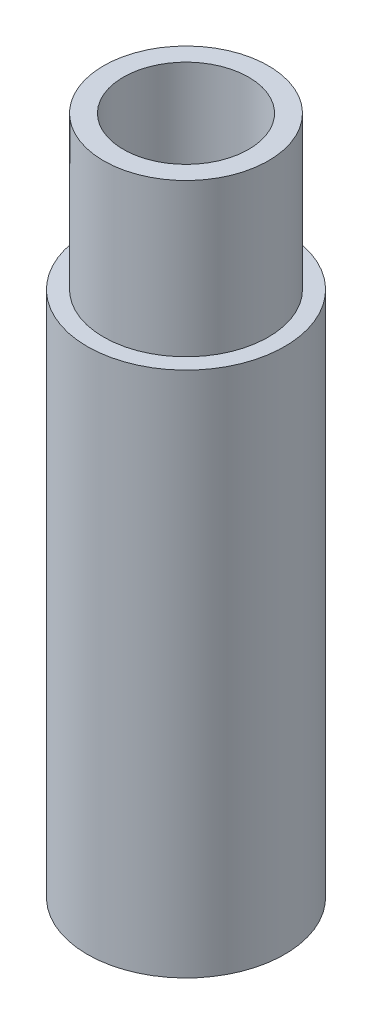
SolidWorks part; units mm, degrees
material "AISI 304"
ref_plane "Front Plane" through (0, 0, 0) normal (0, 0, 1) x (1, 0, 0)
ref_plane "Top Plane" through (0, 0, 0) normal (0, 1, 0) x (1, 0, 0)
ref_plane "Right Plane" through (0, 0, 0) normal (1, 0, 0) x (0, 0, -1)
sketch "Sketch1" plane through (0, 0, 0) normal (0, 1, 0) x (1, 0, 0)
  circle A0 centre (0, 0) radius 4.7625
  dimension "D1" = 9.525
extrude "Boss-Extrude1" add sketch "Sketch1" along normal blind 25.4
sketch "Sketch2" plane through (0, 25.4, 0) normal (0, 1, 0) x (1, 0, 0)
  circle A0 centre (0, 0) radius 3.9751
  dimension "D1" = 7.9502
extrude "Boss-Extrude2" add sketch "Sketch2" along normal blind 7.366
sketch "Sketch3" plane through (0, 0, 0) normal (0, -1, 0) x (1, 0, 0)
  circle A0 centre (0, 0) radius 3.0226
  dimension "D1" = 6.0452
extrude "Cut-Extrude1" cut sketch "Sketch3" against normal through all
sketch "Sketch4" plane through (0, 0, 0) normal (0, -1, 0) x (1, 0, 0)
  circle A0 centre (0, 0) radius 3.4544
  dimension "D1" = 6.9088
hole_wizard "5/16-24 Tapped Hole1" positions "Sketch8" profile "Sketch7" tap size "5/16-24" standard "ANSI Inch"
sketch "Sketch8" plane through (0, 0, 0) normal (0, -1, 0) x (-1, 0, 0)
  point P0 (0, 0)
sketch "Sketch7" plane through (0, 0, 0) normal (1, 0, 0) x (0, 0, -1)
  line L0 (0, 0) -> (0, 14.7756)
  line L1 (0, 14.7756) -> (3.4544, 12.7)
  line L2 (3.4544, 12.7) -> (3.4544, 0)
  line L5 (3.4544, 0) -> (0, 0)
  line L10 (0, 14.7756) -> (-3.4544, 12.7) construction
  line L11 (0, -6.35) -> (0, 107.95) construction
  dimension "Tap Drill Dia." = 6.9088
  dimension "Tap Drill Depth" = 12.7
  dimension "Drill Angle" = 118
cosmetic thread "Hole Thread1" parameters "D1"=12.7, "D2"=7.9375
